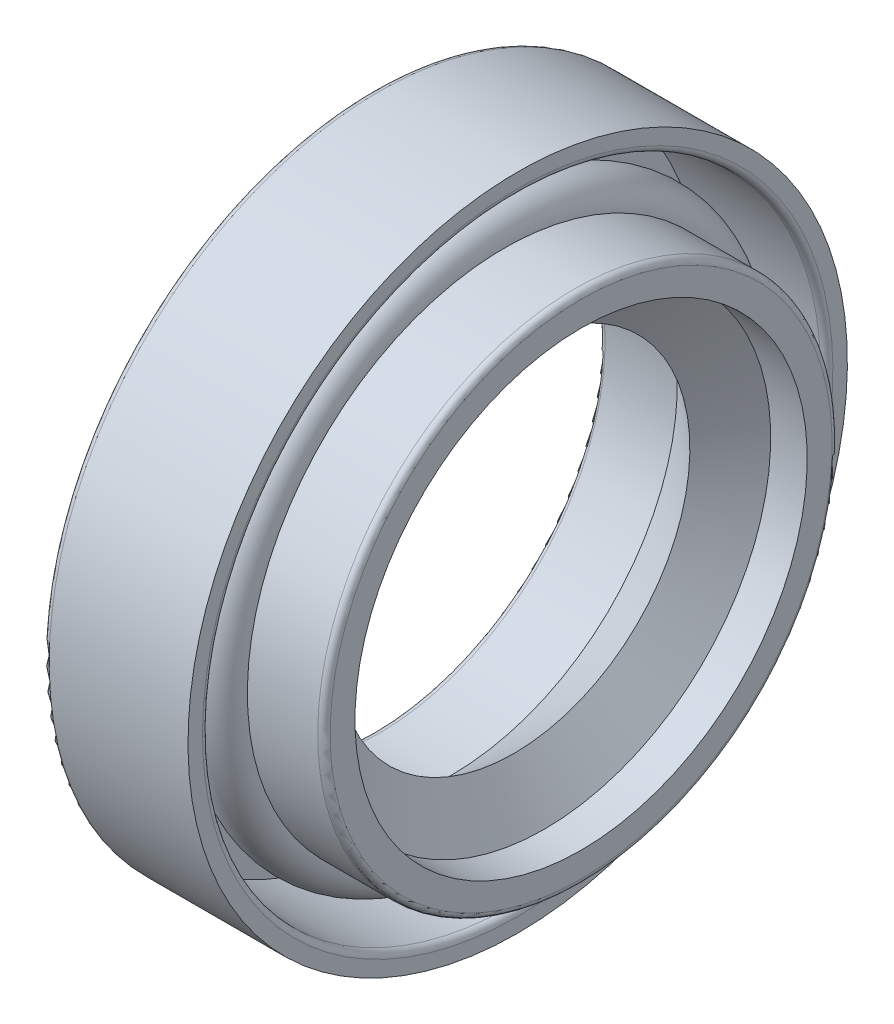
SolidWorks part; units mm, degrees
ref_plane "Front Plane" through (0, 0, 0) normal (0, 0, 1) x (1, 0, 0)
ref_plane "Top Plane" through (0, 0, 0) normal (0, 1, 0) x (1, 0, 0)
ref_plane "Right Plane" through (0, 0, 0) normal (1, 0, 0) x (0, 0, -1)
sketch "Sketch1" plane through (0, 0, 0) normal (0, 0, 1) x (1, 0, 0)
  line L0 (0, 0) -> (28.6636, 0) construction
  line L1 (0, 0) -> (0, 19.6926) construction
  line L2 (0, 15.6141) -> (0, 11.2141)
  line L3 (0.3, 10.9141) -> (3.7935, 10.9141)
  line L4 (3.7935, 10.9141) -> (6.8111, 8.5)
  line L5 (6.8111, 8.5) -> (8.2966, 10.9141)
  line L6 (8.2966, 10.9141) -> (10.0608, 10.9141)
  line L7 (10.0608, 10.9141) -> (10.0608, 12.1141)
  line L8 (9.7608, 12.4141) -> (6.3655, 12.4141)
  line L9 (3.7935, 12.4141) -> (1, 12.4141)
  line L10 (1, 12.4141) -> (1, 14.9141)
  line L11 (1, 14.9141) -> (6.7, 14.9141)
  line L12 (7, 15.2141) -> (7, 15.9141)
  line L13 (7, 15.9141) -> (0.3, 15.9141)
  arc A0 (6.3655, 12.4141) -> (3.7935, 12.4141) centre (5.0795, 12.4141) ccw
  arc A1 (0, 15.6141) -> (0.3, 15.9141) centre (0.3, 15.6141) cw
  arc A2 (0, 11.2141) -> (0.3, 10.9141) centre (0.3, 11.2141) ccw
  arc A3 (10.0608, 12.1141) -> (9.7608, 12.4141) centre (9.7608, 12.1141) ccw
  arc A4 (6.7, 14.9141) -> (7, 15.2141) centre (6.7, 15.2141) ccw
  point P21 (0, 15.9141)
  point P24 (0, 10.9141)
  point P27 (10.0608, 12.4141)
  point P30 (7, 14.9141)
  dimension "D8" = 0.3
  dimension "D1" = 8.5
  dimension "D2" = 5
  dimension "D3" = 2.5
  dimension "D4" = 7
  dimension "D5" = 1
  dimension "D6" = 1
  dimension "D7" = 1.5
revolve "Revolve1" add sketch "Sketch1" angle 360 about L0
